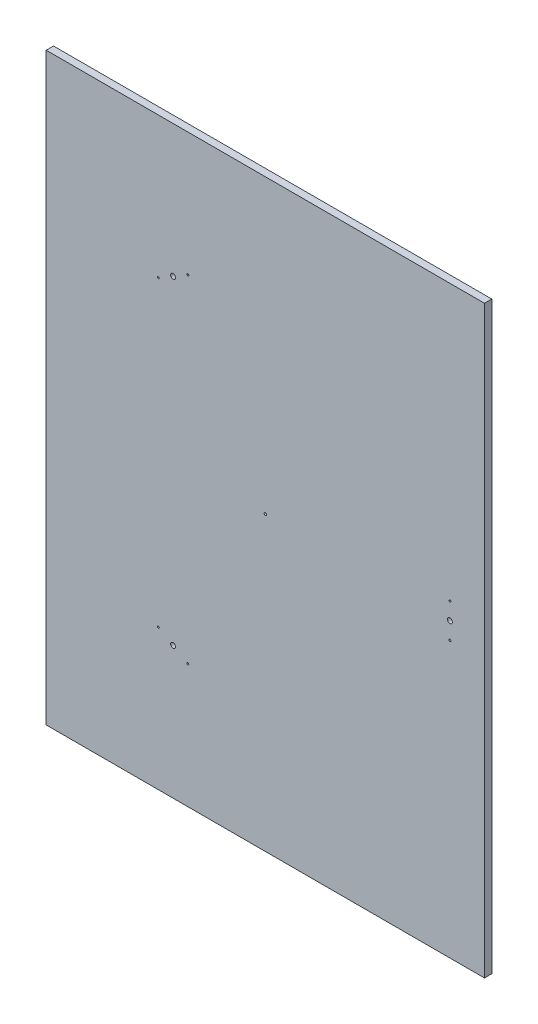
SolidWorks part; units mm, degrees
ref_plane "Plan de face" through (0, 0, 0) normal (0, 0, 1) x (1, 0, 0)
ref_plane "Plan de dessus" through (0, 0, 0) normal (0, 1, 0) x (1, 0, 0)
ref_plane "Plan de droite" through (0, 0, 0) normal (1, 0, 0) x (0, 0, -1)
sketch "Esquisse1" plane through (0, 0, 0) normal (0, 0, 1) x (1, 0, 0)
  line L0 (0, 0) -> (410, 0) construction
  line L1 (379, 112.6409) -> (379, -112.6409) construction
  line L3 (-450, -600) -> (450, -600)
  line L4 (-450, -600) -> (-450, 600)
  line L5 (-450, 600) -> (450, 600)
  line L6 (450, -600) -> (450, 600)
  line L7 (-450, -600) -> (450, 600) construction
  line L8 (-450, 600) -> (450, -600) construction
  circle A1 centre (379, 0) radius 5
  circle A2 centre (379, 35) radius 2
  circle A3 centre (379, -35) radius 2
  circle A4 centre (-189.5, -328.2236) radius 5
  circle A5 centre (-159.1891, -345.7236) radius 2
  circle A6 centre (-219.8109, -310.7236) radius 2
  circle A7 centre (-189.5, 328.2236) radius 5
  circle A8 centre (-219.8109, 310.7236) radius 2
  circle A9 centre (-159.1891, 345.7236) radius 2
  circle A10 centre (0, 0) radius 2.5
  point P27 (0, 0)
  dimension "D1" = 1200
  dimension "D2" = 10
  dimension "D3" = 4
  dimension "D4" = 4
  dimension "D9" = 5
  dimension "D5" = 35
  dimension "D6" = 35
  dimension "D7" = 379
  dimension "D10" = 900
  dimension "D8" = 3
extrude "Boss.-Extru.1" add sketch "Esquisse1" along normal blind 15
